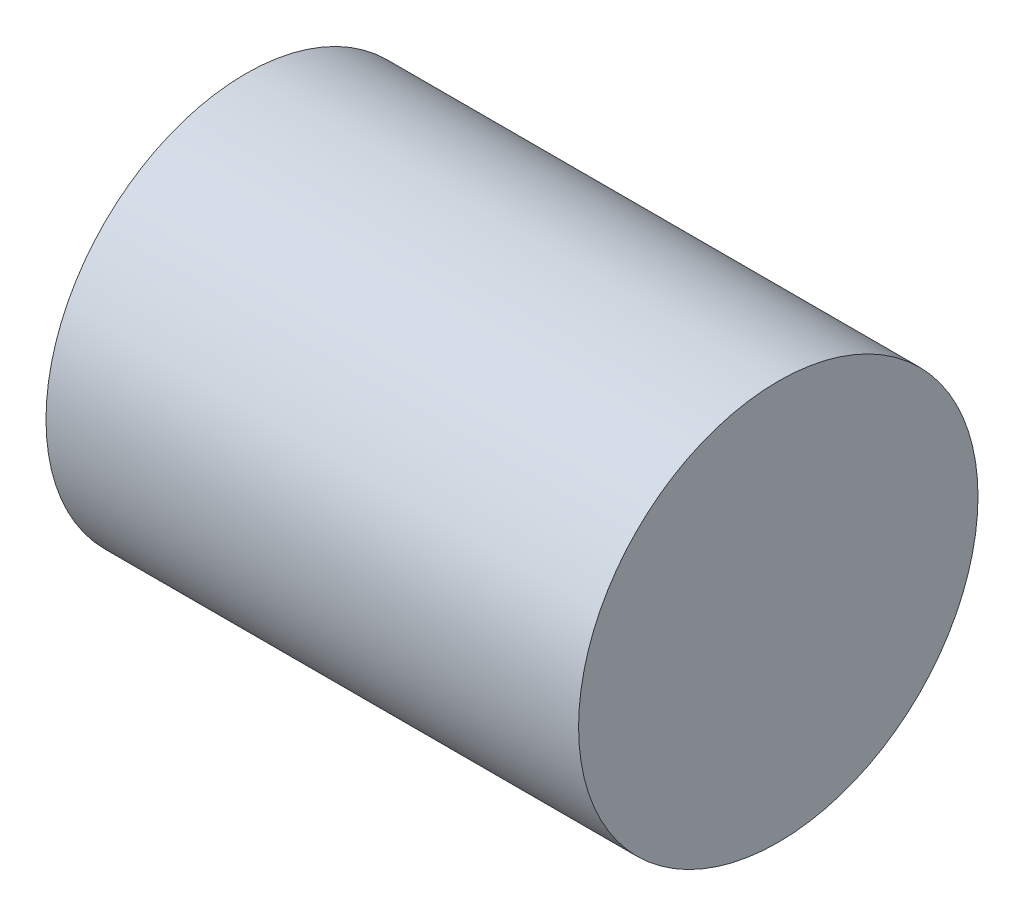
SolidWorks part; units mm, degrees
ref_plane "Front Plane" through (0, 0, 0) normal (0, 0, 1) x (1, 0, 0)
ref_plane "Top Plane" through (0, 0, 0) normal (0, 1, 0) x (1, 0, 0)
ref_plane "Right Plane" through (0, 0, 0) normal (1, 0, 0) x (0, 0, -1)
sketch "Sketch1" plane through (0, 0, 0) normal (1, 0, 0) x (0, 0, -1)
  circle A0 centre (0, 0) radius 15
  dimension "D1" = 30
extrude "Boss-Extrude1" add sketch "Sketch1" against normal blind 40
sketch "Sketch2" plane through (0, 0, 0) normal (0, 1, 0) x (1, 0, 0)
  line L1 (-49.9329, 0) -> (10.449, 0) construction
